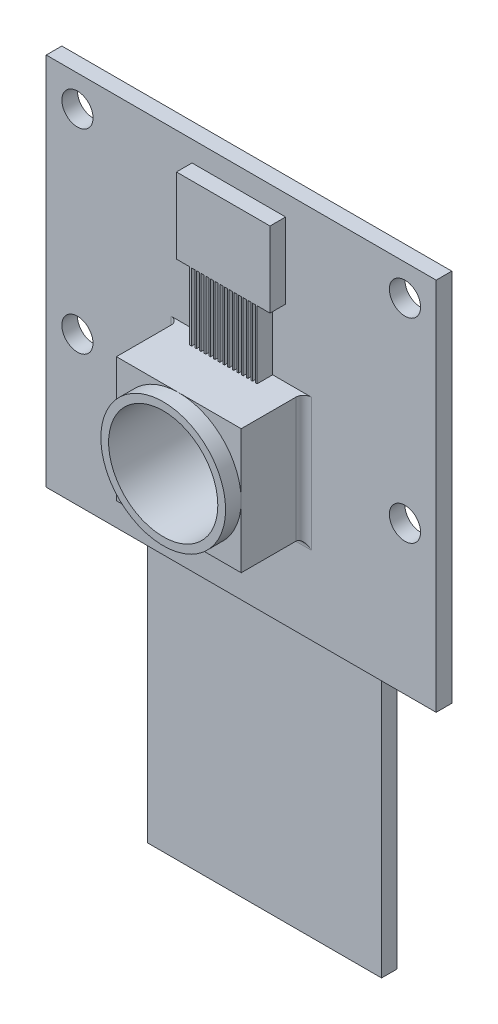
SolidWorks part; units mm, degrees
ref_plane "Front Plane" through (0, 0, 0) normal (0, 0, 1) x (1, 0, 0)
ref_plane "Top Plane" through (0, 0, 0) normal (0, 1, 0) x (1, 0, 0)
ref_plane "Right Plane" through (0, 0, 0) normal (1, 0, 0) x (0, 0, -1)
sketch "Sketch1" plane through (0, 0, 0) normal (0, 0, 1) x (1, 0, 0)
  line L1 (-12.5, 12) -> (12.5, 12)
  line L2 (-12.5, 12) -> (-12.5, -12)
  line L3 (-12.5, -12) -> (12.5, -12)
  line L4 (12.5, 12) -> (12.5, -12)
  line L5 (-12.5, 12) -> (12.5, -12) construction
  line L6 (-12.5, -12) -> (12.5, 12) construction
  circle A0 centre (10.5, 10) radius 1
  circle A1 centre (-10.5, 10) radius 1
  circle A2 centre (-10.5, -2.5) radius 1
  circle A3 centre (10.5, -2.5) radius 1
  point P0 (0, 0)
  dimension "D3" = 2
  dimension "D1" = 24
  dimension "D2" = 25
  dimension "D4" = 2
  dimension "D5" = 2
  dimension "D6" = 2
  dimension "D7" = 2
extrude "Boss-Extrude1" add sketch "Sketch1" along normal blind 1
sketch "Sketch2" plane through (0, 0, 1) normal (0, 0, 1) x (1, 0, 0)
  line L1 (-4, 1.5) -> (4, 1.5)
  line L2 (-4, 1.5) -> (-4, -6.5)
  line L3 (-4, -6.5) -> (4, -6.5)
  line L4 (4, 1.5) -> (4, -6.5)
  line L5 (-4, 1.5) -> (4, -6.5) construction
  line L6 (-4, -6.5) -> (4, 1.5) construction
  point P0 (0, -2.5)
extrude "Boss-Extrude2" add sketch "Sketch2" along normal blind 4
sketch "Sketch3" plane through (0, 0, 5) normal (0, 0, 1) x (1, 0, 0)
  circle A0 centre (0, -2.5) radius 4
extrude "Boss-Extrude3" add sketch "Sketch3" along normal blind 1
fillet "Fillet2" radius 0.5 3 edges at (4, -2.5, 1) (0, -6.5, 1) (-4, -2.5, 1)
sketch "Sketch4" plane through (0, 0, 0) normal (0, 0, -1) x (-1, 0, 0)
  line L0 (12.5, -12) -> (-12.5, -12) construction
  line L1 (-8, -5) -> (8, -5)
  line L2 (-8, -5) -> (-8, -10)
  line L3 (-8, -10) -> (8, -10)
  line L4 (8, -5) -> (8, -10)
  line L5 (-8, -5) -> (8, -10) construction
  line L6 (-8, -10) -> (8, -5) construction
  point P0 (0, 0)
  dimension "D1" = 16
  dimension "D2" = 5
  dimension "D3" = 7
extrude "Boss-Extrude4" add sketch "Sketch4" along normal blind 2
fillet "Fillet3" radius 0.5 12 edges at (0, -5, -2) (0, -5, 0) (0, -10, -2) (0, -10, 0) (8, -5, -1) (8, -7.5, -2) (8, -10, -1) (8, -7.5, 0) (-8, -10, -1) (-8, -7.5, -2) (-8, -5, -1) (-8, -7.5, 0)
sketch "Sketch5" plane through (0, 0, 6) normal (0, 0, 1) x (1, 0, 0)
  circle A0 centre (0, -2.5) radius 3.5
  dimension "D1" = 7
extrude "Cut-Extrude1" cut sketch "Sketch5" against normal blind 6
sketch "Sketch6" plane through (0, 0, 1) normal (0, 0, 1) x (1, 0, 0)
  line L0 (4.5, 1.5) -> (-4.5, 1.5) construction
  line L1 (-3.1525, 5.84) -> (-2.3226, 5.84)
  line L2 (-2.3226, 5.84) -> (-2.3226, 1.5)
  line L3 (-2.3226, 1.5) -> (2.0174, 1.5)
  line L4 (2.0174, 5.84) -> (2.0174, 1.5)
  line L5 (-2.3226, 5.84) -> (2.0174, 1.5) construction
  line L6 (-2.3226, 1.5) -> (2.0174, 5.84) construction
  line L7 (2.6463, 6.4689) -> (2.8469, 6.4689)
  line L8 (-3.1525, 10.68) -> (2.8464, 10.68)
  line L9 (-3.1525, 10.68) -> (-3.1525, 5.84)
  line L10 (-3.152, 6.4689) -> (-2.9515, 6.4689)
  line L11 (2.8464, 10.68) -> (2.8464, 5.84)
  line L12 (-3.1525, 10.68) -> (2.8464, 5.84) construction
  line L13 (-3.1525, 5.84) -> (2.8464, 10.68) construction
  line L14 (2.0174, 5.84) -> (2.8464, 5.84)
  point P0 (-0.1526, 3.67)
  point P7 (-0.1531, 8.26)
  dimension "D1" = 4.34
  dimension "D2" = 4.34
  dimension "D3" = 4.84
extrude "Boss-Extrude5" add sketch "Sketch6" along normal blind 1
sketch "Sketch7" plane through (0, 0, 2) normal (0, 0, 1) x (1, 0, 0)
  line L0 (-2.3226, 1.5) -> (2.0174, 1.5) construction
  line L1 (-2.1726, 1.5) -> (-1.9726, 1.5)
  line L2 (-2.1726, 1.5) -> (-2.1726, 5.84)
  line L3 (-2.1726, 5.84) -> (-1.9726, 5.84)
  line L4 (-1.9726, 1.5) -> (-1.9726, 5.84)
  line L6 (-2.3226, 5.84) -> (-2.3226, 1.5) construction
  dimension "D1" = 0.2
  dimension "D2" = 0.15
extrude "Cut-Extrude2" cut sketch "Sketch7" against normal blind 1
pattern_linear "LPattern1" count 14 spacing 0.3 along (1, 0, 0) of "Cut-Extrude2"
sketch "Sketch8" plane through (0, -10, 0) normal (0, -1, 0) x (1, 0, 0)
  line L1 (-7.5, -1.5) -> (7.5, -1.5)
  line L2 (-7.5, -1.5) -> (-7.5, -0.5)
  line L3 (-7.5, -0.5) -> (7.5, -0.5)
  line L4 (7.5, -1.5) -> (7.5, -0.5)
extrude "Boss-Extrude6" add sketch "Sketch8" along normal blind 20
